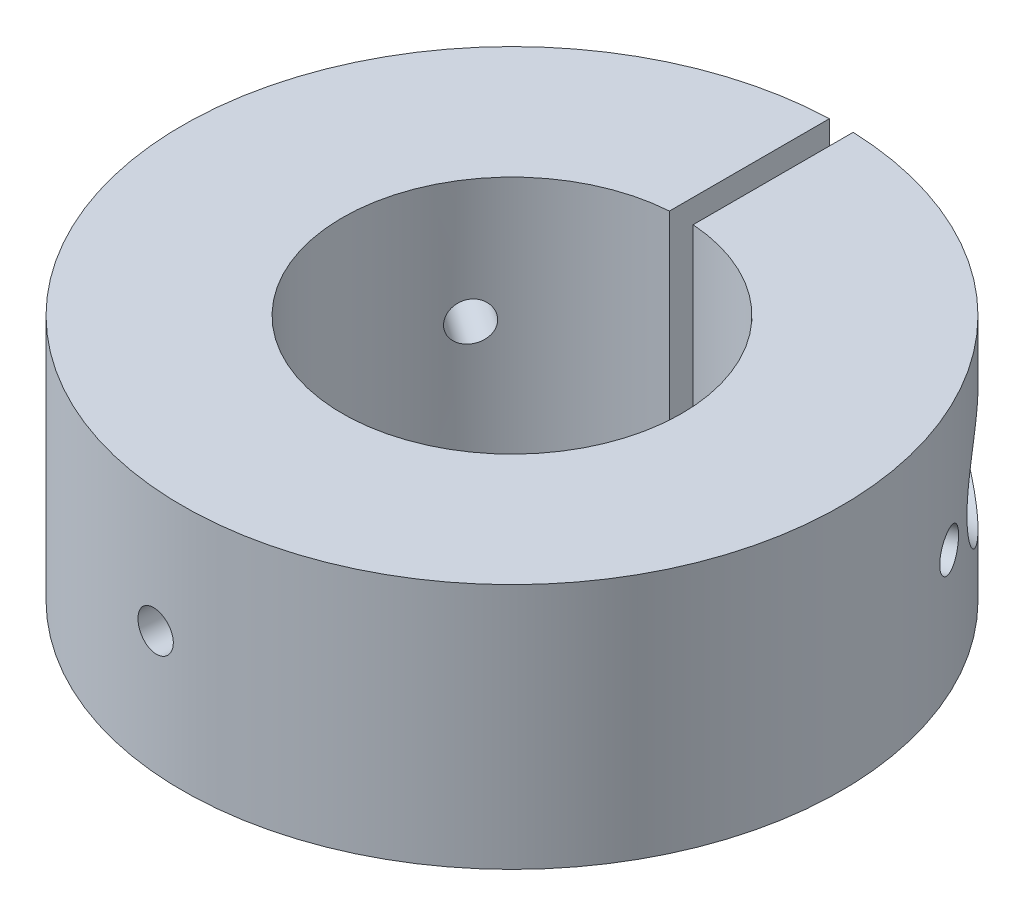
SolidWorks part; units mm, degrees
material "PET"
ref_plane "Front" through (0, 0, 0) normal (0, 0, 1) x (1, 0, 0)
ref_plane "Top" through (0, 0, 0) normal (0, 1, 0) x (1, 0, 0)
ref_plane "Right" through (0, 0, 0) normal (1, 0, 0) x (0, 0, -1)
sketch "Sketch1" plane through (0, 0, 0) normal (0, 1, 0) x (1, 0, 0)
  line L0 (4.143, 19.3357) -> (4.143, 17.6149) construction
  line L1 (4.143, 11.3982) -> (17.8858, 11.3982) construction
  line L2 (4.143, 19.3357) -> (8.715, 19.3357) construction
  line L3 (4.143, 17.6149) -> (0.762, 17.6149) construction
  line L4 (0.762, 17.6149) -> (0.762, 17.0942) construction
  line L5 (0.762, 13.1191) -> (4.143, 13.1191) construction
  line L6 (4.143, 13.1191) -> (4.143, 11.3982) construction
  line L7 (0.762, 17.0942) -> (-12.5543, 17.0942) construction
  line L8 (0.762, 13.6398) -> (0.762, 13.1191) construction
  line L9 (-0.762, 21.1953) -> (-0.762, 10.8954)
  line L10 (0.762, 13.6398) -> (-16.2412, 13.6398) construction
  line L11 (-14.6177, 15.367) -> (14.6177, 15.367) construction
  line L12 (0.762, 10.8954) -> (0.762, 21.1953)
  arc A0 (-0.762, 21.1953) -> (0.762, 21.1953) centre (0, 0) ccw
  arc A1 (-0.762, 10.8954) -> (0.762, 10.8954) centre (0, 0) ccw
  point P19 (0, 0)
  dimension "D1" = 42.418
  dimension "D2" = 21.844
  dimension "D3" = 7.9375
  dimension "D4" = 3.4544
  dimension "D5" = 4.4958
  dimension "D6" = 1.524
  dimension "D7" = 4.572
  dimension "D8" = 4.445
extrude "Boss-Extrude1" add sketch "Sketch1" along normal mid plane 15.875
sketch "Sketch2" plane through (0, 0, 0) normal (0, 1, 0) x (1, 0, 0)
  line L0 (-16.2412, 13.6398) -> (0.762, 13.6398)
  line L1 (0.762, 13.6398) -> (0.762, 13.1191)
  line L2 (0.762, 13.1191) -> (4.143, 13.1191)
  line L3 (4.143, 13.1191) -> (4.143, 11.3982)
  line L4 (4.143, 11.3982) -> (17.8858, 11.3982)
  line L5 (17.8858, 11.3982) -> (17.8858, 15.367)
  line L6 (17.8858, 15.367) -> (-16.2412, 15.367)
  line L7 (-16.2412, 15.367) -> (-16.2412, 13.6398)
  line L8 (-16.2412, 15.367) -> (-19.0327, 15.367) construction
revolve "Cut-Revolve1" cut sketch "Sketch2" angle 360 about L8
hole_wizard "M3x0.5 Tapped Hole1" positions "3DSketch1" profile "Sketch4" tap size "M3x0.5" standard "ANSI Metric"
sketch3d "3DSketch1"
  line L0 (-1.8485, 0, 21.1283) -> (0, 0, 21.1283) construction
  line L1 (0, 0, 21.1283) -> (0, 0, 0) construction
  line L3 (0, 0, 0) -> (-1.8485, 0, 21.1283) construction
  point P0 (-1.8485, 0, 21.1283)
  dimension "D1" = 5
sketch "Sketch4" plane through (-1.8485, 0, 21.1283) normal (0, 1, 0) x (0.9962, 0, 0.0872)
  line L0 (0, 0) -> (0, 10.287)
  line L1 (0, 10.287) -> (1.25, 10.287)
  line L2 (1.25, 10.287) -> (1.25, 0)
  line L5 (1.25, 0) -> (0, 0)
  line L11 (0, -6.35) -> (0, 107.95) construction
  dimension "Thru Tap Drill Dia." = 2.5
  dimension "Thru Tap Drill Depth" = 10.287
cosmetic thread "Hole Thread1" parameters "D2"=3
pattern_circular "CirPattern1" count 3 over 360 about axis through (0, 7.9375, 0) along (0, -1, 0) of "M3x0.5 Tapped Hole1"
cosmetic thread "Hole Thread2" parameters "D2"=3
cosmetic thread "Hole Thread3" parameters "D2"=3
